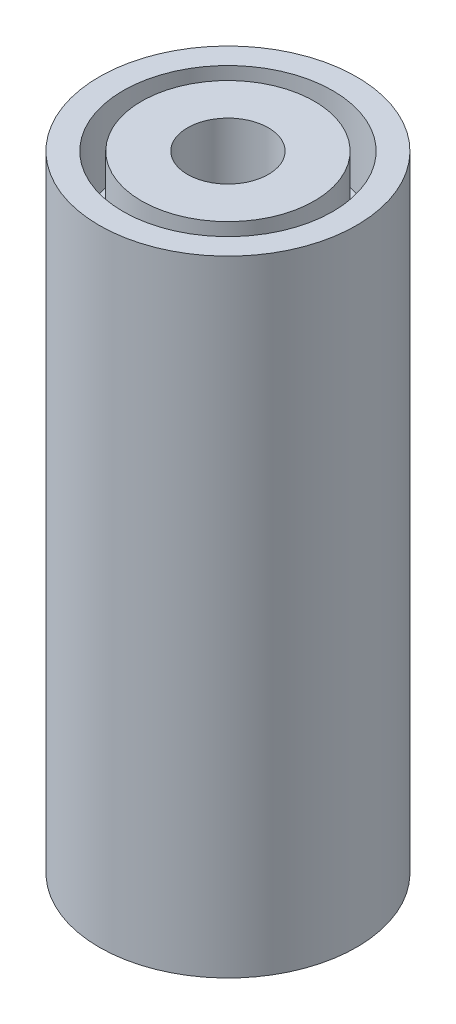
SolidWorks part; units mm, degrees
ref_plane "Plan de face" through (0, 0, 0) normal (0, 0, 1) x (1, 0, 0)
ref_plane "Plan de dessus" through (0, 0, 0) normal (0, 1, 0) x (1, 0, 0)
ref_plane "Plan de droite" through (0, 0, 0) normal (1, 0, 0) x (0, 0, -1)
sketch "Esquisse1" plane through (0, 0, 0) normal (0, 1, 0) x (1, 0, 0)
  circle A0 centre (0, 0) radius 1.1
  circle A1 centre (0, 0) radius 3.5
  dimension "D1" = 2.2
  dimension "D2" = 7
extrude "Boss.-Extru.2" add sketch "Esquisse1" along normal blind 17
sketch "Esquisse2" plane through (0, 17, 0) normal (0, 1, 0) x (1, 0, 0)
  circle A0 centre (0, 0) radius 2.35
  circle A1 centre (0, 0) radius 2.85
  dimension "D1" = 5.7
  dimension "D2" = 0.5
extrude "Enlèv. mat.-Extru.1" cut sketch "Esquisse2" against normal blind 2
